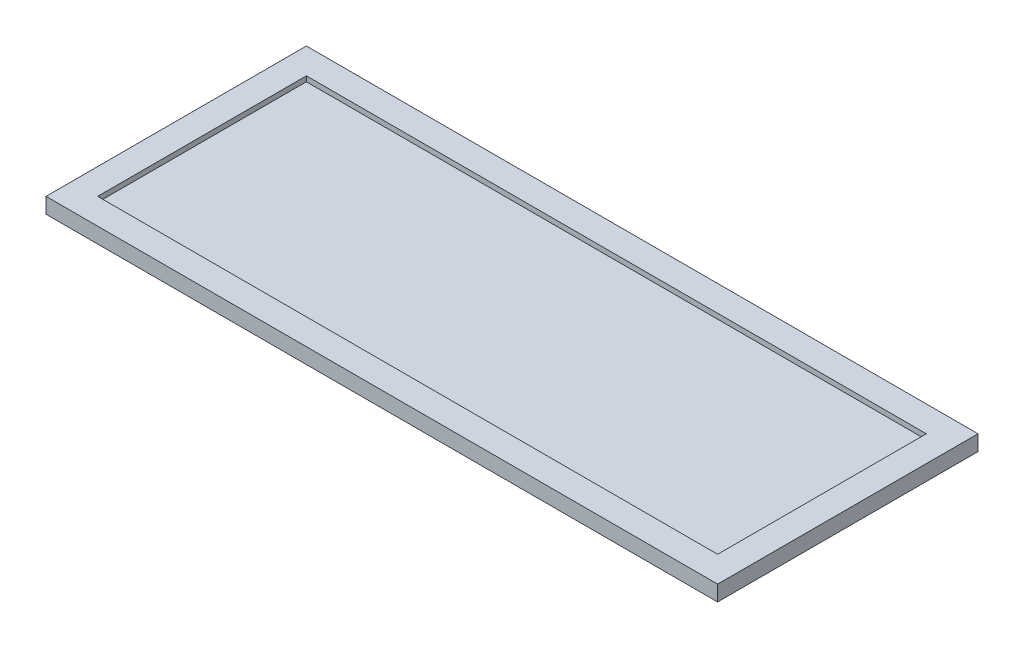
SolidWorks part; units mm, degrees
material "柚木"
ref_plane "前视基准面" through (0, 0, 0) normal (0, 0, 1) x (1, 0, 0)
ref_plane "上视基准面" through (0, 0, 0) normal (0, 1, 0) x (1, 0, 0)
ref_plane "右视基准面" through (0, 0, 0) normal (1, 0, 0) x (0, 0, -1)
sketch "草图1" plane through (0, 0, 0) normal (0, 1, 0) x (1, 0, 0)
  line L0 (300, 101) -> (-300, 101)
  line L1 (325, -126) -> (-325, -126)
  line L2 (325, -126) -> (325, 126)
  line L3 (325, 126) -> (-325, 126)
  line L4 (-325, -126) -> (-325, 126)
  line L5 (325, -126) -> (-325, 126) construction
  line L6 (325, 126) -> (-325, -126) construction
  line L7 (-300, -101) -> (-300, 101)
  line L8 (300, -101) -> (-300, -101)
  line L9 (300, -101) -> (300, 101)
  point P0 (0, 0)
  dimension "D1" = 252
  dimension "D2" = 650
  dimension "D3" = 25
extrude "凸台-拉伸1" add sketch "草图1" along normal mid plane 15
sketch "草图2" plane through (0, 0, 0) normal (0, 1, 0) x (1, 0, 0)
  line L0 (300, 101) -> (-300, 101) construction
  line L3 (-300, 101) -> (-300, -101) construction
  line L4 (-300, -101) -> (300, -101) construction
  line L5 (300, -101) -> (300, 101) construction
  line L6 (300, 101) -> (-300, 101)
  line L7 (-300, 101) -> (-300, -101)
  line L8 (-300, -101) -> (300, -101)
  line L9 (300, -101) -> (300, 101)
extrude "凸台-拉伸2" add sketch "草图2" along normal mid plane 5
